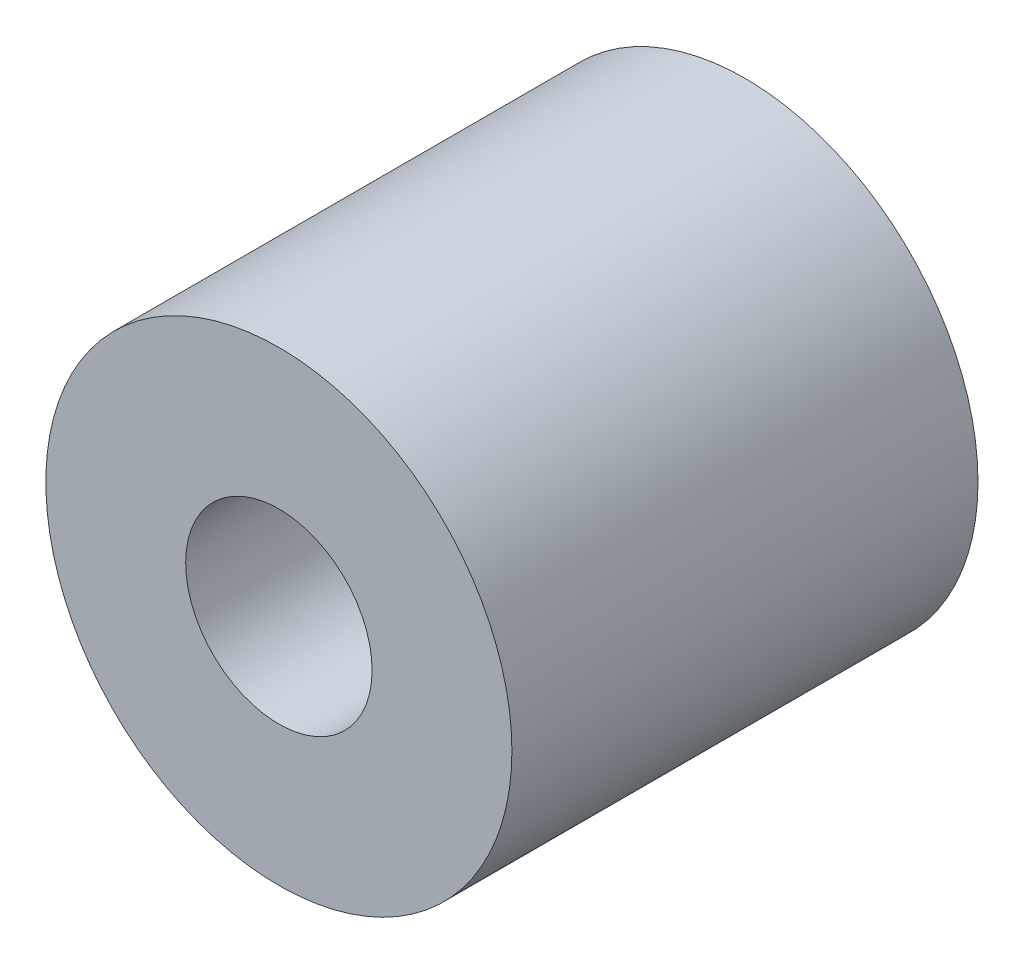
SolidWorks part; units mm, degrees
ref_plane "Plano frontal" through (0, 0, 0) normal (0, 0, 1) x (1, 0, 0)
ref_plane "Plano superior" through (0, 0, 0) normal (0, 1, 0) x (1, 0, 0)
ref_plane "Plano direito" through (0, 0, 0) normal (1, 0, 0) x (0, 0, -1)
sketch "Esboço1" plane through (0, 0, 0) normal (0, 0, 1) x (1, 0, 0)
  circle A0 centre (0, 0) radius 12.5
  circle A2 centre (0, 0) radius 5
  dimension "D1" = 25
  dimension "D2" = 10
extrude "Ressalto-extrusão1" add sketch "Esboço1" along normal blind 25
